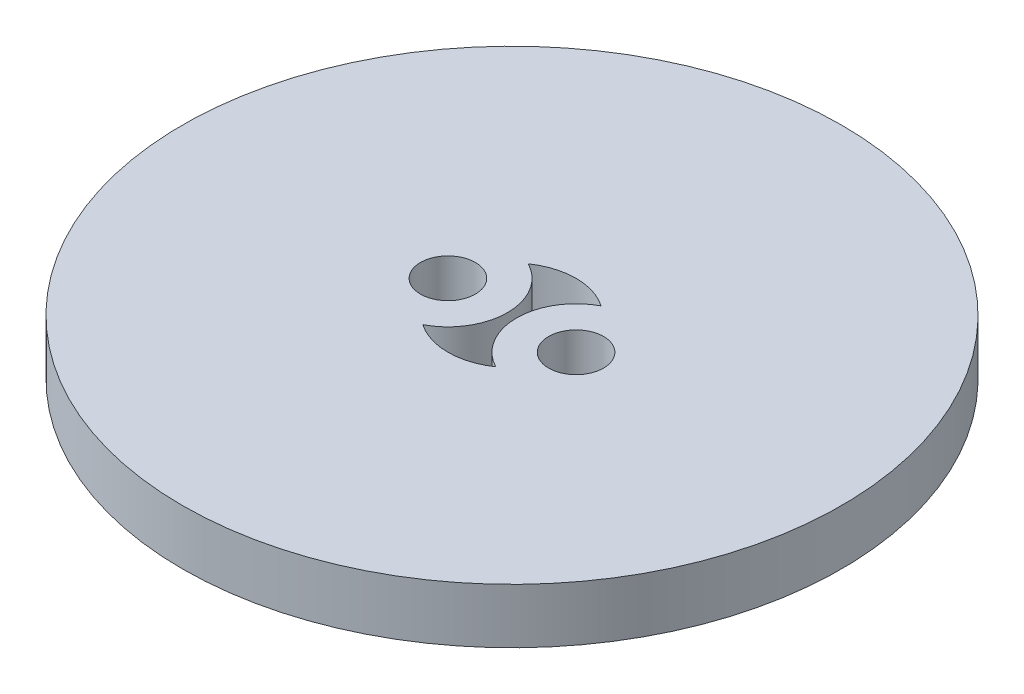
SolidWorks part; units mm, degrees
ref_plane "Plan de face" through (0, 0, 0) normal (0, 0, 1) x (1, 0, 0)
ref_plane "Plan de dessus" through (0, 0, 0) normal (0, 1, 0) x (1, 0, 0)
ref_plane "Plan de droite" through (0, 0, 0) normal (1, 0, 0) x (0, 0, -1)
sketch "Esquisse1" plane through (0, 0, 0) normal (0, 1, 0) x (1, 0, 0)
  line L0 (-3.5, 0) -> (3.5, 0) construction
  circle A0 centre (0, 0) radius 18
  circle A2 centre (-3.5, 0) radius 1.5
  circle A3 centre (3.5, 0) radius 1.5
  arc A4 (1.9911, 2.8785) -> (1.9911, -2.8785) centre (3.5, 0) ccw
  arc A5 (-1.9911, -2.8785) -> (-1.9911, 2.8785) centre (-3.5, 0) ccw
  arc A6 (-1.9911, -2.8785) -> (1.9911, -2.8785) centre (0, 0) ccw
  arc A9 (1.9911, 2.8785) -> (-1.9911, 2.8785) centre (0, 0) ccw
  circle A10 centre (-3.5, 0) radius 3.25 construction
  circle A11 centre (3.5, 0) radius 3.25 construction
  dimension "D1" = 36
  dimension "D2" = 6.5
  dimension "D3" = 6.5
  dimension "D4" = 7
  dimension "D5" = 3
  dimension "D6" = 3
  dimension "D7" = 3.5
  dimension "D8" = 3.5
  dimension "D9" = 3.25
  dimension "D10" = 3.25
  dimension "D11" = 3.5
extrude "Boss.-Extru.1" add sketch "Esquisse1" along normal blind 3
